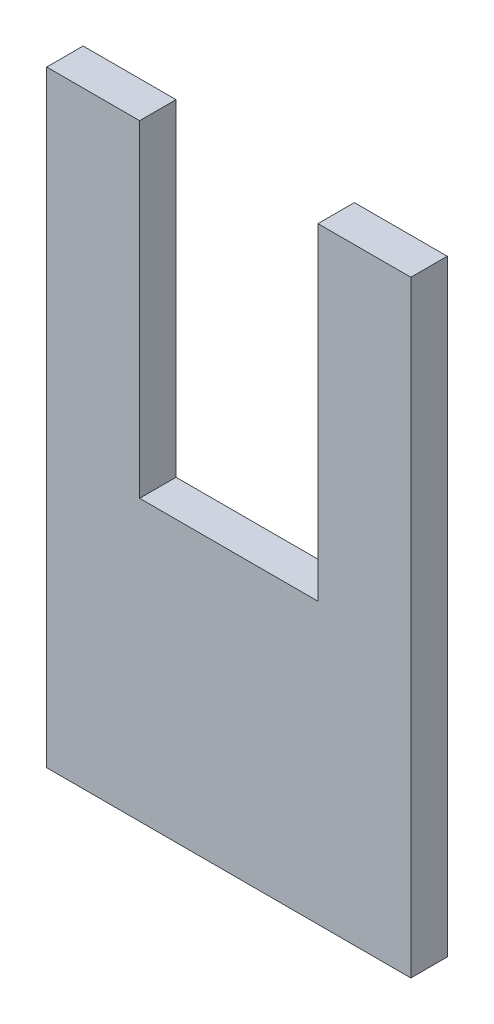
SolidWorks part; units mm, degrees
ref_plane "Plan de face" through (0, 0, 0) normal (0, 0, 1) x (1, 0, 0)
ref_plane "Plan de dessus" through (0, 0, 0) normal (0, 1, 0) x (1, 0, 0)
ref_plane "Plan de droite" through (0, 0, 0) normal (1, 0, 0) x (0, 0, -1)
sketch "Esquisse1" plane through (0, 0, 0) normal (0, 0, 1) x (1, 0, 0)
  line L0 (-55.8242, 43.9702) -> (-48.1704, 43.9702)
  line L1 (-78.1704, 43.9702) -> (-70.5166, 43.9702)
  line L2 (-78.1704, 43.9702) -> (-78.1704, -6.0298)
  line L3 (-78.1704, -6.0298) -> (-48.1704, -6.0298)
  line L4 (-48.1704, 43.9702) -> (-48.1704, -6.0298)
  line L6 (-70.5166, 43.9702) -> (-70.5166, 17.0253)
  line L7 (-70.5166, 17.0253) -> (-55.8242, 17.0253)
  line L8 (-55.8242, 43.9702) -> (-55.8242, 17.0253)
  dimension "D1" = 30
  dimension "D2" = 50
  dimension "D3" = 26.9449
  dimension "D4" = 14.6924
extrude "Boss.-Extru.1" add sketch "Esquisse1" along normal blind 3
